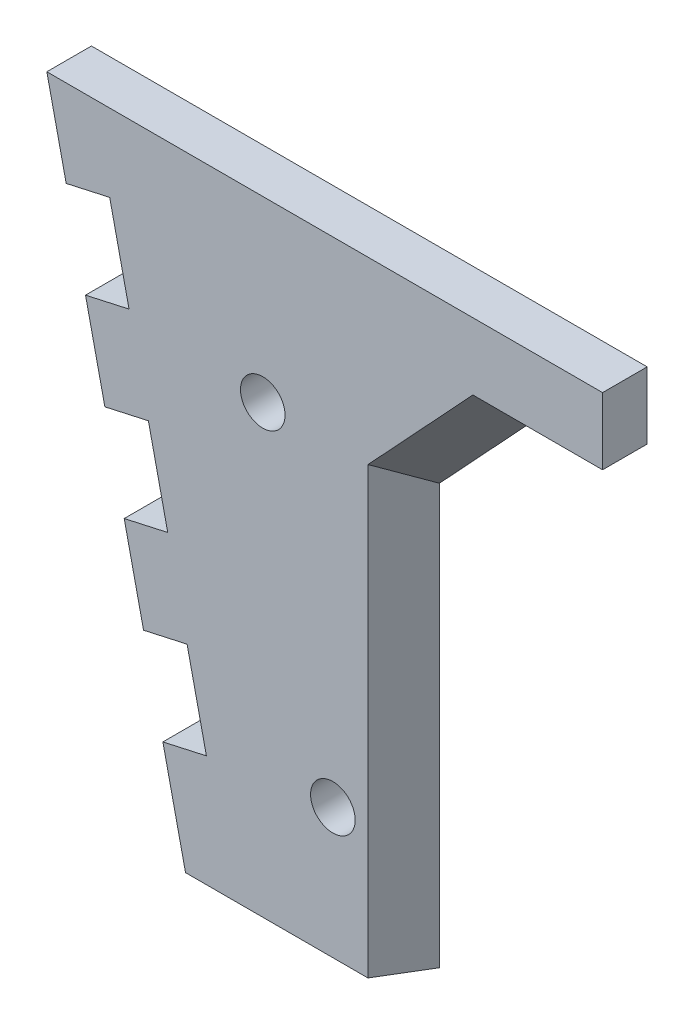
SolidWorks part; units mm, degrees
ref_plane "Front Plane" through (0, 0, 0) normal (0, 0, 1) x (1, 0, 0)
ref_plane "Top Plane" through (0, 0, 0) normal (0, 1, 0) x (1, 0, 0)
ref_plane "Right Plane" through (0, 0, 0) normal (1, 0, 0) x (0, 0, -1)
sketch "Sketch1" plane through (0, 0, 0) normal (0, 0, 1) x (1, 0, 0)
  line L0 (-48.4221, 40) -> (-17.3205, -100)
  line L1 (-48.4221, 40) -> (54.7707, 40)
  line L2 (-17.3205, -100) -> (29.6277, -100)
  line L3 (18.4113, 40) -> (-30, 40) construction
  line L5 (-48.4221, 40) -> (-88.6977, 40) construction
  line L6 (-16.4664, 74.1213) -> (36.4115, -163.9022) construction
  line L7 (29.6277, -100) -> (29.6277, -5.8949)
  line L8 (31.9345, -3.417) -> (0.0856, -37.6284) construction
  line L9 (72.3534, 40) -> (29.6277, -5.8949)
  line L10 (72.3534, 40) -> (54.7707, 40)
  circle A0 centre (0, 0) radius 5
  circle A3 centre (0, 0) radius 5 construction
extrude "Boss-Extrude1" add sketch "Sketch1" along normal blind 10
sketch "Sketch2" plane through (0, 0, 0) normal (0, 0, -1) x (-1, 0, 0)
  line L0 (44.0847, 20.476) -> (34.3227, 22.6446)
  line L1 (48.4221, 40) -> (17.3205, -100) construction
  line L2 (38.1783, 40) -> (7.0767, -100) construction
  line L3 (-72.3534, 40) -> (48.4221, 40) construction
  line L4 (17.3205, -100) -> (-29.6277, -100) construction
  line L5 (39.7474, 0.952) -> (29.9854, 3.1206)
  line L6 (25.648, -16.4034) -> (35.4101, -18.5721)
  line L7 (21.3107, -35.9274) -> (31.0727, -38.0961)
  line L8 (16.9734, -55.4514) -> (26.7354, -57.6201)
  line L9 (12.636, -74.9755) -> (22.398, -77.1441)
  line L10 (34.3227, 22.6446) -> (29.9854, 3.1206)
  line L11 (25.648, -16.4034) -> (21.3107, -35.9274)
  line L12 (16.9734, -55.4514) -> (12.636, -74.9755)
  line L13 (26.7354, -57.6201) -> (22.398, -77.1441)
  line L14 (35.4101, -18.5721) -> (31.0727, -38.0961)
  line L15 (44.0847, 20.476) -> (39.7474, 0.952)
  dimension "D1" = 20
  dimension "D2" = 20
  dimension "D3" = 20
  dimension "D4" = 20
  dimension "D5" = 20
  dimension "D6" = 20
  dimension "D7" = 10
extrude "Cut-Extrude1" cut sketch "Sketch2" against normal blind 10
sketch "Sketch3" plane through (11.2034, -10.4297, 12.6142) normal (-0.5648, 0.5258, -0.636) x (-0.8252, -0.3599, 0.4353)
  line L0 (-74.1031, 30.8273) -> (-22.3271, -4.5431)
  line L1 (-22.3271, -4.5431) -> (-17.974, 1.8291)
  line L2 (-4.4441, 21.6343) -> (-66.9144, 64.3105)
  line L3 (-55.6198, -63.1331) -> (8.5239, 43.1146) construction
  line L4 (-66.9144, 64.3105) -> (-84.7974, 38.1331)
  line L5 (-84.7974, 38.1331) -> (-74.1031, 30.8273)
  line L6 (-17.974, 1.8291) -> (-4.4441, 21.6343)
extrude "Cut-Extrude2" cut sketch "Sketch3" against normal blind 10
ref_plane "Plane1" through (21.724, 0, 13.1034) normal (-0.8563, 0, -0.5165) x (-0.5165, 0, 0.8563)
sketch "Sketch4" plane through (21.724, 0, 13.1034) normal (-0.8563, 0, -0.5165) x (-0.5165, 0, 0.8563)
  line L0 (-3.6243, -0.2797) -> (-15.3026, -5.8949)
  line L1 (-15.3026, -5.8949) -> (-15.3026, -100)
  line L2 (-15.3026, -100) -> (-3.6243, -100)
  line L3 (-3.6243, -100) -> (-3.6243, -0.2797)
extrude "Cut-Extrude3" cut sketch "Sketch4" against normal blind 10
sketch "Sketch5" plane through (0, 40, 0) normal (0, 1, 0) x (1, 0, 0)
  line L0 (72.3534, 0) -> (76.206, 0)
  line L1 (76.206, 0) -> (76.206, -10)
  line L2 (76.206, -10) -> (61.0941, -10)
  line L3 (61.0941, -10) -> (61.0941, 0) construction
  line L4 (72.3534, 0) -> (-48.4221, 0) construction
  line L5 (61.0941, 0) -> (72.3534, 0)
  line L6 (61.0941, -10) -> (39.8438, -10)
  line L7 (61.0941, -10) -> (-48.4221, -10) construction
  line L8 (39.8438, -10) -> (39.8438, 0)
  line L9 (39.8438, 0) -> (61.0941, 0)
extrude "Boss-Extrude2" add sketch "Sketch5" against normal up to surface (15 mm away)
sketch "Sketch6" plane through (0, 0, 0) normal (0, 0, -1) x (-1, 0, 0)
  circle A0 centre (-15.7229, -70.7746) radius 5
  dimension "D1" = 10
extrude "Cut-Extrude4" cut sketch "Sketch6" against normal blind 10
